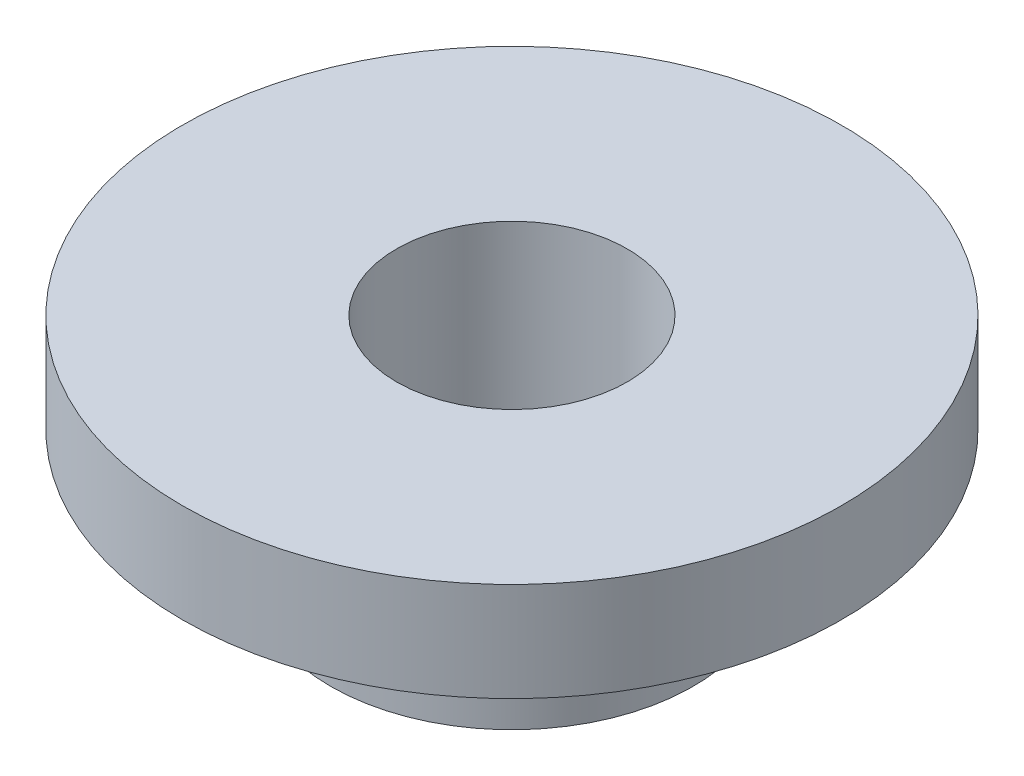
SolidWorks part; units mm, degrees
ref_plane "Front Plane" through (0, 0, 0) normal (0, 0, 1) x (1, 0, 0)
ref_plane "Top Plane" through (0, 0, 0) normal (0, 1, 0) x (1, 0, 0)
ref_plane "Right Plane" through (0, 0, 0) normal (1, 0, 0) x (0, 0, -1)
sketch "Sketch1" plane through (0, 0, 0) normal (0, 1, 0) x (1, 0, 0)
  line L0 (0, 0) -> (0, 57.15) construction
  circle A0 centre (0, 0) radius 57.15
  circle A1 centre (0, 6.35) radius 1.397
  circle A2 centre (0, 25.4) radius 3.175
  circle A3 centre (0, 50.8) radius 3.175
  circle A4 centre (25.4, 0) radius 3.175
  circle A5 centre (0, -25.4) radius 3.175
  circle A6 centre (-25.4, 0) radius 3.175
  circle A7 centre (6.35, 0) radius 1.397
  circle A8 centre (0, -6.35) radius 1.397
  circle A9 centre (-6.35, 0) radius 1.397
  circle A10 centre (35.921, 35.921) radius 3.175
  circle A11 centre (50.8, 0) radius 3.175
  circle A12 centre (35.921, -35.921) radius 3.175
  circle A13 centre (0, -50.8) radius 3.175
  circle A14 centre (-35.921, -35.921) radius 3.175
  circle A15 centre (-50.8, 0) radius 3.175
  circle A16 centre (-35.921, 35.921) radius 3.175
  point P19 (0, 0)
  point P26 (0, 0)
  point P40 (0, 0)
  dimension "D1" = 114.3
  dimension "D5" = 2.794
  dimension "D6" = 6.35
  dimension "D2" = 6.35
  dimension "D3" = 25.4
  dimension "D4" = 50.8
  dimension "D7" = 4
  dimension "D8" = 4
  dimension "D9" = 8
extrude "Boss-Extrude1" add sketch "Sketch1" along normal blind 4.572
sketch "Sketch2" plane through (0, 4.572, 0) normal (0, 1, 0) x (1, 0, 0)
  circle A0 centre (-25.4, 0) radius 2.75
  circle A1 centre (-25.4, 0) radius 1.75
  dimension "D1" = 3.5
  dimension "D2" = 5.5
extrude "Boss-Extrude2" add sketch "Sketch2" against normal blind 2 separate body
sketch "Sketch3" plane through (0, 4.572, 0) normal (0, 1, 0) x (1, 0, 0)
  circle A0 centre (-25.4, 0) radius 5
  circle A2 centre (-25.4, 0) radius 1.75 construction
  circle A3 centre (-25.4, 0) radius 1.75
  dimension "D1" = 10
extrude "Boss-Extrude3" add sketch "Sketch3" along normal blind 1.5
delete or keep bodies "Body-Delete/Keep 1" type keep bodies bodies 103
